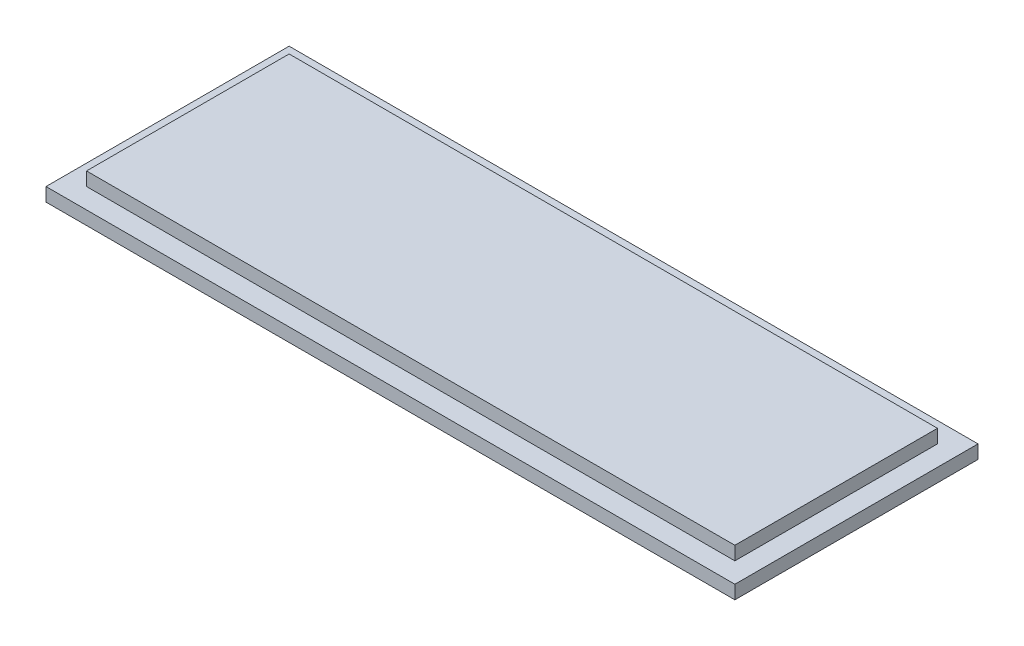
SolidWorks part; units mm, degrees
ref_plane "前视基准面" through (0, 0, 0) normal (0, 0, 1) x (1, 0, 0)
ref_plane "上视基准面" through (0, 0, 0) normal (0, 1, 0) x (1, 0, 0)
ref_plane "右视基准面" through (0, 0, 0) normal (1, 0, 0) x (0, 0, -1)
other "Configuration Table"
sketch "草图2" plane through (0, 0, 0) normal (0, 1, 0) x (1, 0, 0)
  line L1 (-25.5, -9) -> (25.5, -9)
  line L2 (-25.5, -9) -> (-25.5, 9)
  line L3 (-25.5, 9) -> (25.5, 9)
  line L4 (25.5, -9) -> (25.5, 9)
  line L5 (-25.5, -9) -> (25.5, 9) construction
  line L6 (-25.5, 9) -> (25.5, -9) construction
  point P0 (0, 0)
  dimension "D1" = 18
  dimension "D2" = 51
extrude "凸台-拉伸1" add sketch "草图2" along normal blind 1
sketch "草图3" plane through (0, 1, 0) normal (0, 1, 0) x (1, 0, 0)
  line L1 (-24, 7.5) -> (24, 7.5)
  line L2 (-24, 7.5) -> (-24, -7.5)
  line L3 (-24, -7.5) -> (24, -7.5)
  line L4 (25.5, -9) -> (25.5, 9)
  line L5 (25.5, 9) -> (-25.5, 9)
  line L6 (-25.5, 9) -> (-25.5, -9)
  line L7 (-25.5, -9) -> (25.5, -9)
  line L8 (25.5, -9) -> (25.5, 9) construction
  line L9 (25.5, 9) -> (-25.5, 9) construction
  line L10 (-25.5, 9) -> (-25.5, -9) construction
  line L11 (-25.5, -9) -> (25.5, -9) construction
  line L12 (24, 7.5) -> (24, -7.5)
  line L13 (-24, 7.5) -> (24, -7.5) construction
  line L14 (-24, -7.5) -> (24, 7.5) construction
  point P2 (0, 0)
  dimension "D2" = 15
  dimension "D3" = 48
  dimension "D1" = 0
extrude "凸台-拉伸2" add sketch "草图3" along normal blind 1
